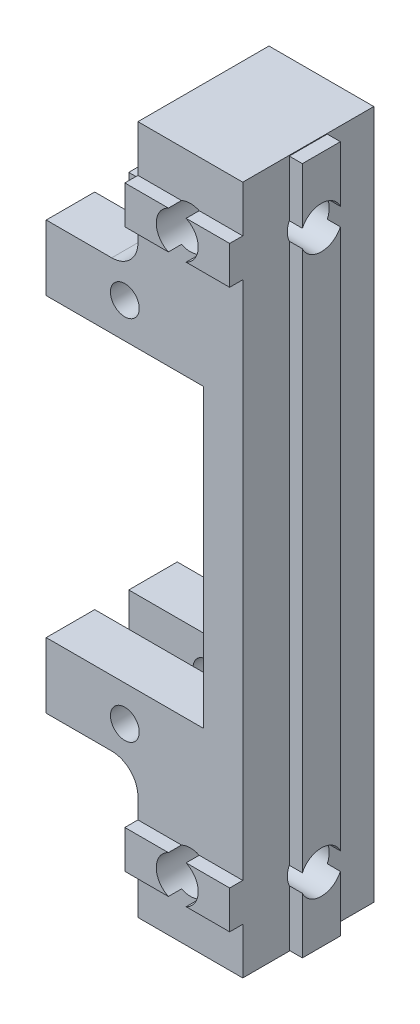
SolidWorks part; units mm, degrees
ref_plane "Front Plane" through (0, 0, 0) normal (0, 0, 1) x (1, 0, 0)
ref_plane "Top Plane" through (0, 0, 0) normal (0, 1, 0) x (1, 0, 0)
ref_plane "Right Plane" through (0, 0, 0) normal (1, 0, 0) x (0, 0, -1)
sketch "Sketch1" plane through (0, 0, 0) normal (0, 0, 1) x (1, 0, 0)
  line L0 (0, 11.3) -> (-12, 11.3)
  line L1 (-12, 11.3) -> (-12, 16.3)
  line L2 (-12, 16.3) -> (-5, 16.3)
  line L3 (3, 26.3) -> (3, -26.3)
  line L4 (-12, -16.3) -> (-5, -16.3)
  line L5 (-12, -16.3) -> (-12, -11.3)
  line L6 (-12, -11.3) -> (0, -11.3)
  line L7 (0, -11.3) -> (0, 11.3)
  line L8 (-6, 14) -> (-6, -14) construction
  line L9 (-5, 16.3) -> (-5, 26.3)
  line L10 (-5, 26.3) -> (3, 26.3)
  line L11 (-5, -16.3) -> (-5, -26.3)
  line L12 (-5, -26.3) -> (3, -26.3)
  circle A0 centre (-6, 14) radius 1.1
  circle A1 centre (-6, -14) radius 1.1
  point P10 (0, 0)
  point P12 (-6, -11.3)
  point P15 (-6, 0)
  dimension "D5" = 2.2
  dimension "D1" = 22.6
  dimension "D2" = 12
  dimension "D3" = 3
  dimension "D4" = 5
  dimension "D6" = 28
  dimension "D7" = 10
  dimension "D8" = 8
extrude "Main" add sketch "Sketch1" along normal mid plane 10
sketch "Sketch2" plane through (0, 0, 0) normal (0, 1, 0) x (1, 0, 0)
  line L0 (3, -5) -> (3, 5) construction
  line L1 (3, 1.45) -> (4, 1.45)
  line L2 (3, 1.45) -> (3, -1.45)
  line L3 (3, -1.45) -> (4, -1.45)
  line L4 (4, 1.45) -> (4, -1.45)
  line L5 (3, -5) -> (-5, -5) construction
  dimension "D1" = 1
  dimension "D2" = 2.9
  dimension "D3" = 3.55
extrude "MakerBeamSupport" add sketch "Sketch2" along normal mid plane 52.5
sketch "Sketch3" plane through (-5, 0, 0) normal (-1, 0, 0) x (0, 0, 1)
  line L1 (0, -55) -> (0, 55) construction
  line L3 (-5, 26.3) -> (-5, 16.3) construction
  line L4 (-5, -16.3) -> (-5, -26.3) construction
  circle A0 centre (0, 21.3) radius 1.6
  circle A1 centre (0, -21.3) radius 1.6
  point P5 (-5, 21.3)
  point P6 (-5, -21.3)
  dimension "D1" = 3.2
extrude "MakerBeamHoles" cut sketch "Sketch3" against normal through all
sketch "Sketch4" plane through (-12, 0, 0) normal (-1, 0, 0) x (0, 0, 1)
  line L0 (5, 16.3) -> (-5, 16.3) construction
  line L1 (-1.3, 16.3) -> (1.3, 16.3)
  line L2 (-1.3, 16.3) -> (-1.3, -16.3)
  line L3 (-1.3, -16.3) -> (1.3, -16.3)
  line L4 (1.3, 16.3) -> (1.3, -16.3)
  line L5 (5, -16.3) -> (-5, -16.3) construction
  line L7 (-5, 16.3) -> (-5, 11.3) construction
  line L8 (5, 16.3) -> (5, 11.3) construction
  dimension "D1" = 2.6
  dimension "D2" = 3.7
  dimension "D3" = 3.7
extrude "Cut-Extrude2" cut sketch "Sketch4" against normal up to surface (12 mm away) up to face at (0, 0, 0)
sketch "Sketch5" plane through (0, 0, 5) normal (0, 0, -1) x (-1, 0, 0)
  line L1 (-3, 22.75) -> (5, 22.75)
  line L2 (-3, 22.75) -> (-3, 19.85)
  line L3 (-3, 19.85) -> (5, 19.85)
  line L4 (5, 22.75) -> (5, 19.85)
  line L7 (5, -19.85) -> (-3, -19.85)
  line L8 (5, -19.85) -> (5, -22.75)
  line L9 (5, -22.75) -> (-3, -22.75)
  line L10 (-3, -19.85) -> (-3, -22.75)
  line L13 (5, 26.3) -> (5, 16.3) construction
  line L15 (-3, -26.3) -> (-3, 26.3) construction
  line L16 (-3, 26.3) -> (5, 26.3) construction
  line L17 (5, -26.3) -> (-3, -26.3) construction
  line L18 (5, 16.3) -> (12, 16.3) construction
  dimension "D1" = 2.9
  dimension "D2" = 3.55
  dimension "D3" = 0
  dimension "D4" = 3.55
  dimension "D5" = 3.55
extrude "MakerBeamTopSupport" add sketch "Sketch5" against normal blind 1
sketch "Sketch6" plane through (0, 0, 6) normal (0, 0, 1) x (1, 0, 0)
  line L6 (3, 26.3) -> (-5, 26.3) construction
  line L9 (-5, 19.85) -> (-5, 22.75) construction
  line L11 (-5, -22.75) -> (-5, -19.85) construction
  circle A0 centre (-1, 21.3) radius 1.6
  circle A1 centre (-1, -21.3) radius 1.6
  point P5 (-5, 21.3)
  point P9 (-5, -21.3)
  point P13 (-1, 26.3)
  dimension "D1" = 3.2
extrude "MakerBeamTopHolesSupport" cut sketch "Sketch6" against normal through all
fillet "Fillet1" radius 2 4 edges at (-5, 16.3, 3.15) (-5, 16.3, -3.15) (-5, -16.3, 3.15) (-5, -16.3, -3.15)
